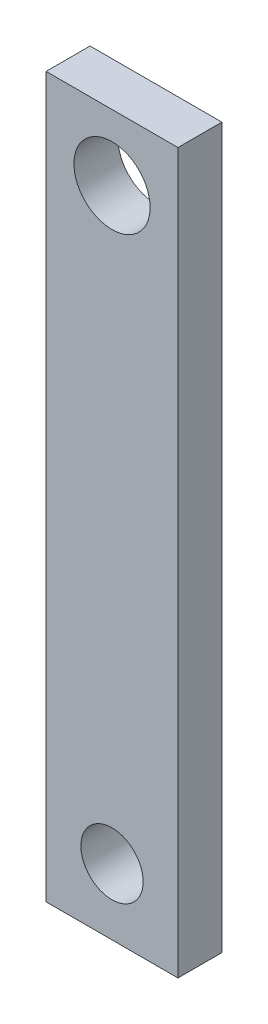
SolidWorks part; units mm, degrees
material "Copper"
ref_plane "Front" through (0, 0, 0) normal (0, 0, 1) x (1, 0, 0)
ref_plane "Top" through (0, 0, 0) normal (0, 1, 0) x (1, 0, 0)
ref_plane "Right" through (0, 0, 0) normal (1, 0, 0) x (0, 0, -1)
sketch "Sketch1" plane through (0, 0, 0) normal (0, 0, 1) x (1, 0, 0)
  line L0 (0, -127.142) -> (0, -42.306) construction
  line L1 (0, -127.142) -> (0, -42.306) construction
  line L3 (9.525, -136.667) -> (-9.525, -136.667)
  line L4 (9.525, -136.667) -> (9.525, -32.781)
  line L5 (9.525, -32.781) -> (-9.525, -32.781)
  line L6 (-9.525, -136.667) -> (-9.525, -32.781)
  point P6 (0, 0)
  point P7 (0, -136.667)
  dimension "D1" = 9.525
  dimension "D2" = 9.525
  dimension "D3" = 19.05
extrude "Boss-Extrude1" add sketch "Sketch1" along normal blind 6.35 contours L4 L5 L6 L3
hole_wizard "M8 Clearance Hole1" positions "Sketch2" profile "Sketch3" hole size "M8" standard "ANSI Metric"
sketch "Sketch2" plane through (0, 0, 6.35) normal (0, 0, 1) x (1, 0, 0)
  point P0 (0, -127.142)
  point P5 (0, 0)
  point P6 (0, 0)
  point P8 (0, 0)
  point P10 (0, 0)
sketch "Sketch3" plane through (0, -127.142, 6.35) normal (1, 0, 0) x (0, -1, 0)
  line L0 (0, 0) -> (0, 23.7859)
  line L1 (0, 23.7859) -> (4.5, 21.082)
  line L2 (4.5, 21.082) -> (4.5, 0)
  line L5 (4.5, 0) -> (0, 0)
  line L10 (0, 23.7859) -> (-4.5, 21.082) construction
  line L11 (0, -6.35) -> (0, 107.95) construction
  dimension "Hole Dia." = 9
  dimension "Hole Depth" = 21.082
  dimension "Drill Angle" = 118
hole_wizard "M10 Clearance Hole1" positions "Sketch4" profile "Sketch5" hole size "M10" standard "ANSI Metric"
sketch "Sketch4" plane through (0, 0, 6.35) normal (0, 0, 1) x (1, 0, 0)
  point P0 (0, -42.306)
  point P3 (0, 0)
sketch "Sketch5" plane through (0, -42.306, 6.35) normal (1, 0, 0) x (0, -1, 0)
  line L0 (0, 0) -> (0, 24.3867)
  line L1 (0, 24.3867) -> (5.5, 21.082)
  line L2 (5.5, 21.082) -> (5.5, 0)
  line L5 (5.5, 0) -> (0, 0)
  line L10 (0, 24.3867) -> (-5.5, 21.082) construction
  line L11 (0, -6.35) -> (0, 107.95) construction
  dimension "Hole Dia." = 11
  dimension "Hole Depth" = 21.082
  dimension "Drill Angle" = 118
